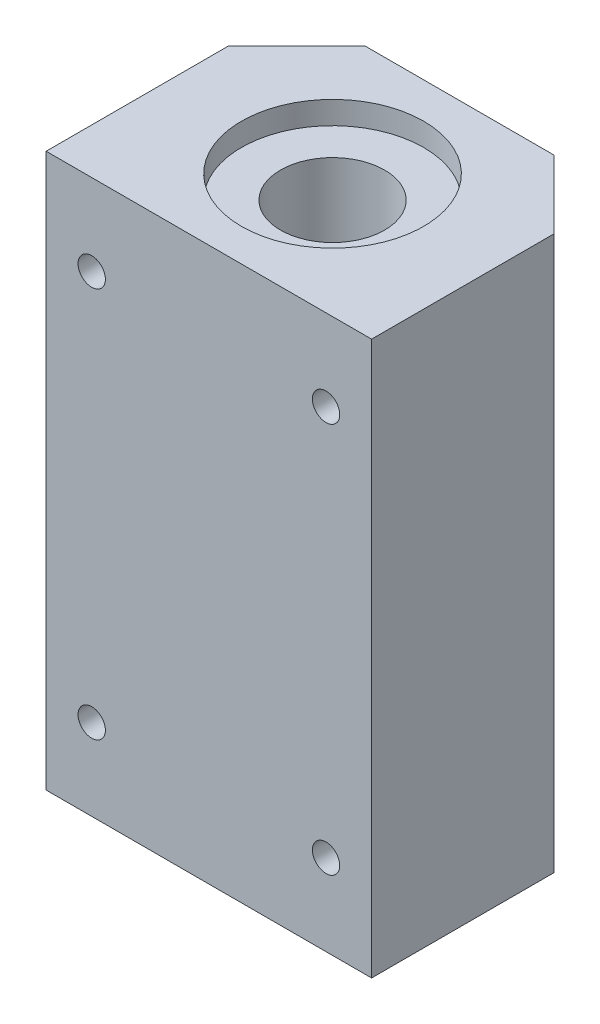
SolidWorks part; units mm, degrees
ref_plane "Front Plane" through (0, 0, 0) normal (0, 0, 1) x (1, 0, 0)
ref_plane "Top Plane" through (0, 0, 0) normal (0, 1, 0) x (1, 0, 0)
ref_plane "Right Plane" through (0, 0, 0) normal (1, 0, 0) x (0, 0, -1)
sketch "Sketch1" plane through (0, 0, 0) normal (0, 0, 1) x (1, 0, 0)
  line L1 (-25, 42.5) -> (25, 42.5)
  line L2 (-25, 42.5) -> (-25, -42.5)
  line L3 (-25, -42.5) -> (25, -42.5)
  line L4 (25, 42.5) -> (25, -42.5)
  line L5 (-25, 42.5) -> (25, -42.5) construction
  line L6 (-25, -42.5) -> (25, 42.5) construction
  point P0 (0, 0)
  dimension "D1" = 85
  dimension "D2" = 50
extrude "Boss-Extrude1" add sketch "Sketch1" along normal blind 38.5
hole_wizard "M5 Tapped Hole1" positions "Sketch4" profile "Sketch5" tap size "M5" standard "ISO" end condition through all
sketch "Sketch4" plane through (0, 0, 38.5) normal (0, 0, 1) x (1, 0, 0)
  line L0 (-25, 0) -> (25, 0) construction
  line L1 (-25, 42.5) -> (-25, -42.5) construction
  line L2 (25, -42.5) -> (25, 42.5) construction
  line L4 (25, 42.5) -> (-25, 42.5) construction
  line L5 (0, 42.5) -> (0, -42.5) construction
  line L6 (-25, -42.5) -> (25, -42.5) construction
  point P0 (-18, 30)
  point P2 (18, 30)
  point P4 (18, -30)
  point P6 (-18, -30)
  dimension "D1" = 36
  dimension "D2" = 60
sketch "Sketch5" plane through (-18, 30, 38.5) normal (1, 0, 0) x (0, -1, 0)
  line L0 (0, 0) -> (0, 38.5)
  line L1 (0, 38.5) -> (2.1, 38.5)
  line L2 (2.1, 38.5) -> (2.1, 0)
  line L5 (2.1, 0) -> (0, 0)
  line L11 (0, -6.35) -> (0, 107.95) construction
  dimension "Thru Tap Drill Dia." = 4.2
  dimension "Thru Tap Drill Depth" = 38.5
cosmetic thread "Hole Thread1" parameters "D2"=5
cosmetic thread "Hole Thread2" parameters "D2"=5
cosmetic thread "Hole Thread3" parameters "D2"=5
cosmetic thread "Hole Thread4" parameters "D2"=5
sketch "Sketch6" plane through (0, 42.5, 0) normal (0, 1, 0) x (1, 0, 0)
  line L0 (-25, -10.5) -> (-14.5, 0)
  line L1 (-25, -38.5) -> (-25, 0) construction
  line L2 (25, 0) -> (-25, 0) construction
  line L3 (-25, -10.5) -> (-25, 0)
  line L4 (-25, 0) -> (-14.5, 0)
  line L5 (0, 0) -> (0, -38.5) construction
  line L6 (25, -38.5) -> (-25, -38.5) construction
  line L7 (25, -10.5) -> (14.5, 0)
  line L8 (25, 0) -> (14.5, 0)
  line L9 (25, -10.5) -> (25, 0)
  circle A0 centre (0, -19.5) radius 14
  dimension "D3" = 28
  dimension "D4" = 19
  dimension "D1" = 45
  dimension "D2" = 10.5
extrude "Cut-Extrude1" cut sketch "Sketch6" against normal through all
ref_plane "Plane1" through (0, 0, 0) normal (0, -1, 0) x (-1, 0, 0)
sketch "Sketch8" plane through (0, 0, 0) normal (0, -1, 0) x (-1, 0, 0)
  circle A0 centre (0, -19.5) radius 8
  circle A1 centre (0, -19.5) radius 14 construction
  circle A2 centre (0, -19.5) radius 14
  dimension "D1" = 16
  dimension "D2" = 28
extrude "Boss-Extrude2" add sketch "Sketch8" along normal mid plane 78
